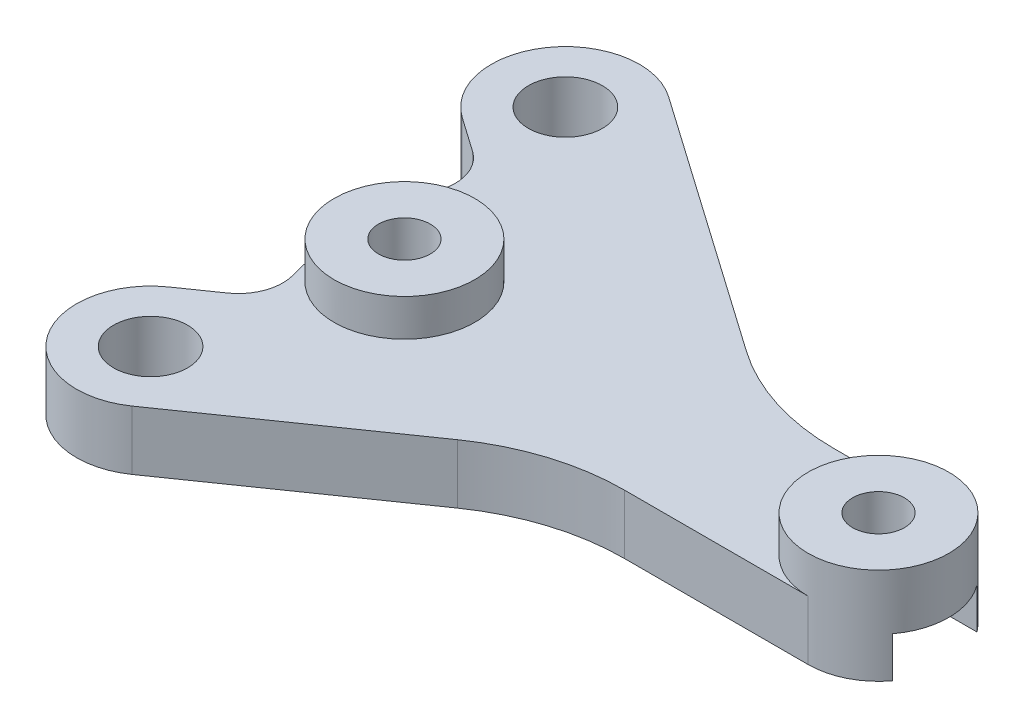
SolidWorks part; units mm, degrees
ref_plane "Front Plane" through (0, 0, 0) normal (0, 0, 1) x (1, 0, 0)
ref_plane "Top Plane" through (0, 0, 0) normal (0, 1, 0) x (1, 0, 0)
ref_plane "Right Plane" through (0, 0, 0) normal (1, 0, 0) x (0, 0, -1)
sketch "Sketch1" plane through (0, 0, 0) normal (0, 1, 0) x (1, 0, 0)
  line L0 (-33.7438, 11.7872) -> (-29.5589, 8.8577)
  line L1 (-50, 25) -> (50, 25)
  line L2 (-50, 25) -> (-50, -25)
  line L3 (-50, -25) -> (50, -25)
  line L4 (50, 25) -> (50, -25)
  line L5 (-33.7334, -8.0133) -> (-29.5538, -5.1034)
  line L6 (-28.0091, 19.9795) -> (-6.587, 4.984)
  line L7 (-28.0196, -16.2201) -> (-11.2087, -4.516)
  line L8 (-26.0922, 0.234) -> (5.9078, 0.234) construction
  line L9 (5.9078, -4.516) -> (-11.2087, -4.516)
  line L10 (-6.587, 4.984) -> (5.9078, 4.984)
  circle A0 centre (-30.8765, 15.8833) radius 2.5
  circle A1 centre (-30.8765, -12.1167) radius 2.5
  circle A2 centre (26.788, 7.9643) radius 2.2
  arc A4 (-28.0091, 19.9795) -> (-33.7438, 11.7872) centre (-30.8765, 15.8833) ccw
  arc A5 (-33.7334, -8.0133) -> (-28.0196, -16.2201) centre (-30.8765, -12.1167) ccw
  arc A6 (-29.5589, 8.8577) -> (-29.5538, -5.1034) centre (-12.6823, 1.8833) ccw
  arc A7 (-28.1758, 20.0912) -> (-33.5771, 11.6754) centre (-30.8765, 15.8833) ccw construction
  arc A8 (-33.5771, -7.9088) -> (-28.1758, -16.3246) centre (-30.8765, -12.1167) ccw construction
  circle A15 centre (-26.0922, 0.234) radius 1.75
  circle A16 centre (5.9078, 0.234) radius 1.75
  circle A17 centre (-26.0922, 0.234) radius 4.75 construction
  arc A18 (5.9078, -4.516) -> (5.9078, 4.984) centre (5.9078, 0.234) ccw
  circle A21 centre (-26.0922, 0.234) radius 1.75 construction
  circle A22 centre (5.9078, 0.234) radius 4.75 construction
  point P4 (0, -25)
  point P6 (-50, 0)
  point P23 (-24.5492, -11.9961)
  dimension "D4" = 3
  dimension "D1" = 50
  dimension "D2" = 100
extrude "Boss-Extrude1" add sketch "Sketch1" along normal blind 4
sketch "Sketch3" plane through (0, 4, 0) normal (0, 1, 0) x (1, 0, 0)
  circle A0 centre (-26.0922, 0.234) radius 4.75
  circle A1 centre (5.9078, 0.234) radius 4.75
  circle A2 centre (-26.0922, 0.234) radius 1.75
  circle A3 centre (5.9078, 0.234) radius 1.75
extrude "Boss-Extrude2" add sketch "Sketch3" along normal blind 2.5
fillet "Fillet1" radius 3 2 edges at (-29.5538, 2, 5.1034) (-29.5589, 2, -8.8577)
fillet "Fillet2" radius 15 2 edges at (-6.587, 2, -4.984) (-11.2087, 2, 4.516)
sketch "Sketch4" plane through (0, 0, 0) normal (0, -1, 0) x (1, 0, 0)
  line L0 (11.5101, -0.234) -> (-35.4479, -0.234) construction
  line L1 (11.5101, -3.084) -> (-35.4479, -3.084)
  line L2 (11.5101, -3.084) -> (11.5101, 2.616)
  line L3 (11.5101, 2.616) -> (-35.4479, 2.616)
  line L4 (-35.4479, -3.084) -> (-35.4479, 2.616)
  line L5 (5.9078, -0.234) -> (5.9078, -6.0079) construction
  arc A1 (-2.629, 2.616) -> (-2.629, -3.084) centre (5.9078, -0.234) ccw
  arc A2 (-17.5554, -3.084) -> (-17.5554, 2.616) centre (-26.0922, -0.234) ccw
  circle M8 centre (-26.0922, -0.234) radius 1.75
  circle M9 centre (5.9078, -0.234) radius 1.75
  arc M16 (-30.2454, 3.1168) -> (-30.2472, -6.8771) centre (-12.6823, -1.8833) ccw
  arc M23 (5.9078, -4.984) -> (5.9078, 4.516) centre (5.9078, -0.234) ccw
  dimension "D2" = 18
  dimension "D1" = 5.7
extrude "Cut-Extrude1" cut sketch "Sketch4" against normal blind 2.75 contours L3 A1 L1 M23 M9 | L1 A2 L3 M16 M8
